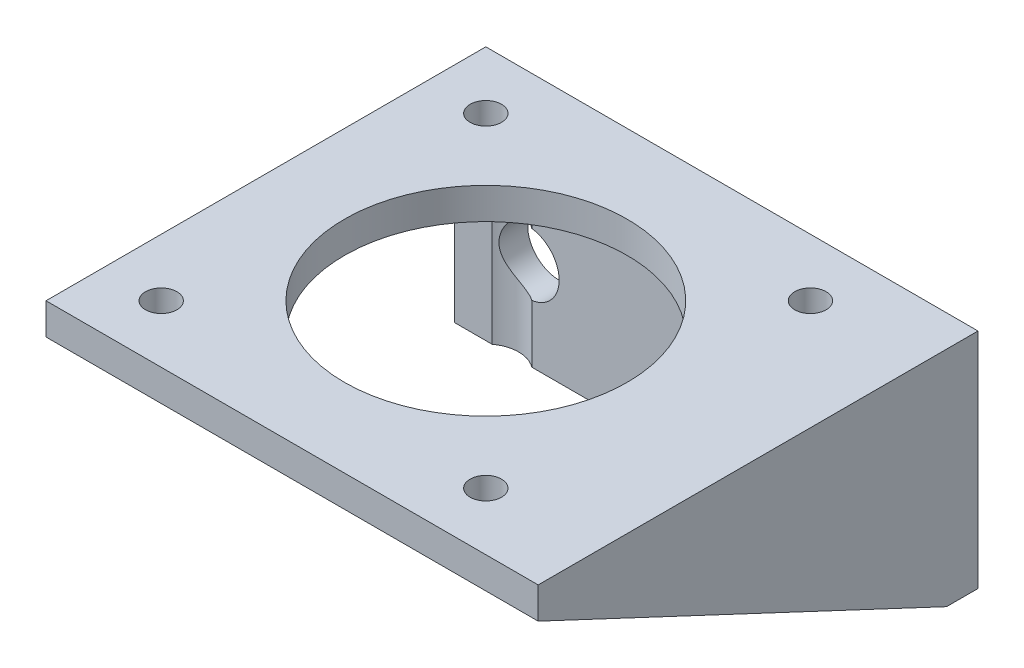
SolidWorks part; units mm, degrees
material "ABS"
ref_plane "Front Plane" through (0, 0, 0) normal (0, 0, 1) x (1, 0, 0)
ref_plane "Top Plane" through (0, 0, 0) normal (0, 1, 0) x (1, 0, 0)
ref_plane "Right Plane" through (0, 0, 0) normal (1, 0, 0) x (0, 0, -1)
sketch "Sketch1" plane through (0, 0, 0) normal (0, 0, 1) x (1, 0, 0)
  line L1 (77.1448, 157.566) -> (119.1448, 157.566)
  line L2 (77.1448, 157.566) -> (77.1448, 178.866)
  line L3 (77.1448, 178.866) -> (119.1448, 178.866)
  line L4 (119.1448, 157.566) -> (119.1448, 178.866)
  dimension "D1" = 42
  dimension "D2" = 21.3
extrude "Boss-Extrude1" add sketch "Sketch1" along normal blind 3
sketch "Sketch2" plane through (0, 0, 3) normal (0, 0, 1) x (1, 0, 0)
  line L0 (119.1448, 166.066) -> (77.1448, 166.066) construction
  line L1 (119.1448, 157.566) -> (119.1448, 178.866) construction
  line L2 (77.1448, 178.866) -> (77.1448, 157.566) construction
  line L3 (77.1448, 157.566) -> (119.1448, 157.566) construction
  circle A0 centre (112.1448, 166.066) radius 3
  circle A1 centre (84.1448, 166.066) radius 3
  dimension "D2" = 6
  dimension "D1" = 8.5
  dimension "D3" = 7
  dimension "D4" = 7
extrude "Cut-Extrude1" cut sketch "Sketch2" against normal blind 3
sketch "Sketch4" plane through (0, 178.866, 0) normal (0, 1, 0) x (-1, 0, 0)
  line L0 (-119.1448, 3) -> (-119.1448, 0) construction
  line L1 (-119.1448, 0) -> (-77.1448, 0)
  line L2 (-119.1448, 0) -> (-119.1448, 42)
  line L3 (-119.1448, 42) -> (-77.1448, 42)
  line L4 (-77.1448, 0) -> (-77.1448, 42)
  line L5 (-82.6448, 36.5002) -> (-113.6448, 36.5002) construction
  line L6 (-113.6448, 36.5002) -> (-113.6448, 5.5002) construction
  line L7 (-113.6448, 5.5002) -> (-82.6448, 5.5002) construction
  line L8 (-82.6448, 5.5002) -> (-82.6448, 36.5002) construction
  line L9 (-98.1448, 21.0002) -> (-98.1448, 5.5002) construction
  line L10 (-98.1448, 5.5002) -> (-98.1448, 0) construction
  circle A2 centre (-113.6448, 36.5002) radius 1.5
  circle A3 centre (-82.6448, 36.5002) radius 1.5
  circle A4 centre (-82.6448, 5.5002) radius 1.5
  circle A5 centre (-113.6448, 5.5002) radius 1.5
  circle A6 centre (-98.1448, 21.0002) radius 13.5
  point P9 (-119.1448, 42)
  dimension "D7" = 3
  dimension "D8" = 27
  dimension "D1" = 42
  dimension "D3" = 5.5002
  dimension "D4" = 15.5
  dimension "D5" = 31
  dimension "D6" = 31
extrude "Boss-Extrude2" add sketch "Sketch4" against normal blind 3
sketch "Sketch5" plane through (119.1448, 0, 0) normal (1, 0, 0) x (0, 0, -1)
  line L0 (0, 157.566) -> (0, 178.866)
  line L1 (0, 157.566) -> (0, 178.866) construction
  line L2 (0, 178.866) -> (-42, 178.866)
  line L4 (-42, 178.866) -> (0, 178.866) construction
  line L5 (-42, 178.866) -> (-42, 175.866)
  line L6 (-42, 175.866) -> (-3, 157.566)
  line L7 (-3, 157.566) -> (-3, 175.866) construction
  line L8 (-3, 157.566) -> (0, 157.566)
  line L9 (-42, 178.866) -> (0, 178.866) construction
extrude "Boss-Extrude3" add sketch "Sketch5" along normal blind 5
sketch "Sketch6" plane through (0, 175.866, 0) normal (0, -1, 0) x (1, 0, 0)
  circle A0 centre (82.6448, 5.5002) radius 3.1343
  circle A1 centre (113.6448, 5.5002) radius 3.1343
extrude "Cut-Extrude2" cut sketch "Sketch6" along normal blind 20
